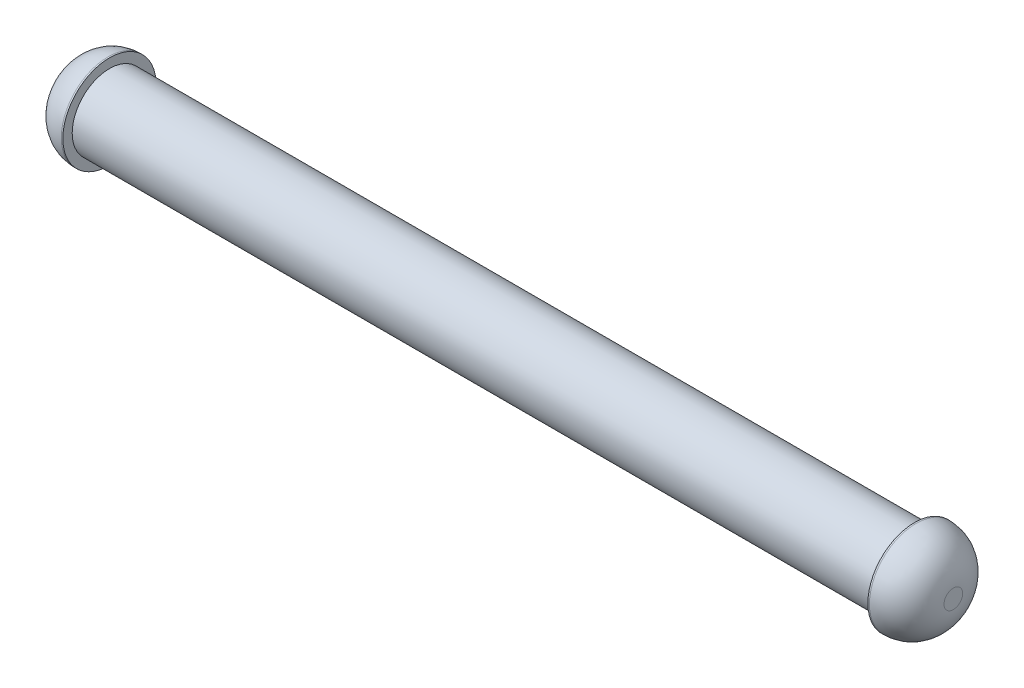
SolidWorks part; units mm, degrees
material "1060 Alloy"
ref_plane "Front Plane" through (0, 0, 0) normal (0, 0, 1) x (1, 0, 0)
ref_plane "Top Plane" through (0, 0, 0) normal (0, 1, 0) x (1, 0, 0)
ref_plane "Right Plane" through (0, 0, 0) normal (1, 0, 0) x (0, 0, -1)
sketch "Sketch1" plane through (0, 0, 0) normal (0, 1, 0) x (1, 0, 0)
  line L0 (-71, 0) -> (71, 0) construction
  line L1 (0, 0) -> (0, 96.6088) construction
  line L2 (-71, 0) -> (-71, 7.5)
  line L3 (-71, 7.5) -> (-64.75, 7.5)
  line L4 (-64.75, 7.5) -> (-64.75, 6)
  line L5 (-64.75, 6) -> (64.75, 6)
  line L6 (-71, 0) -> (71, 0)
  line L7 (64.75, 7.5) -> (64.75, 6)
  line L8 (71, 7.5) -> (64.75, 7.5)
  line L9 (71, 0) -> (71, 7.5)
  point P10 (0, 6)
  dimension "D1" = 64.75
  dimension "D2" = 6.25
  dimension "D3" = 6
  dimension "D4" = 7.5
revolve "Revolve1" add sketch "Sketch1" angle 360 about L6
fillet "Fillet1" radius 6 2 edges at (-71, 0, 7.5) (71, 0, 7.5)
